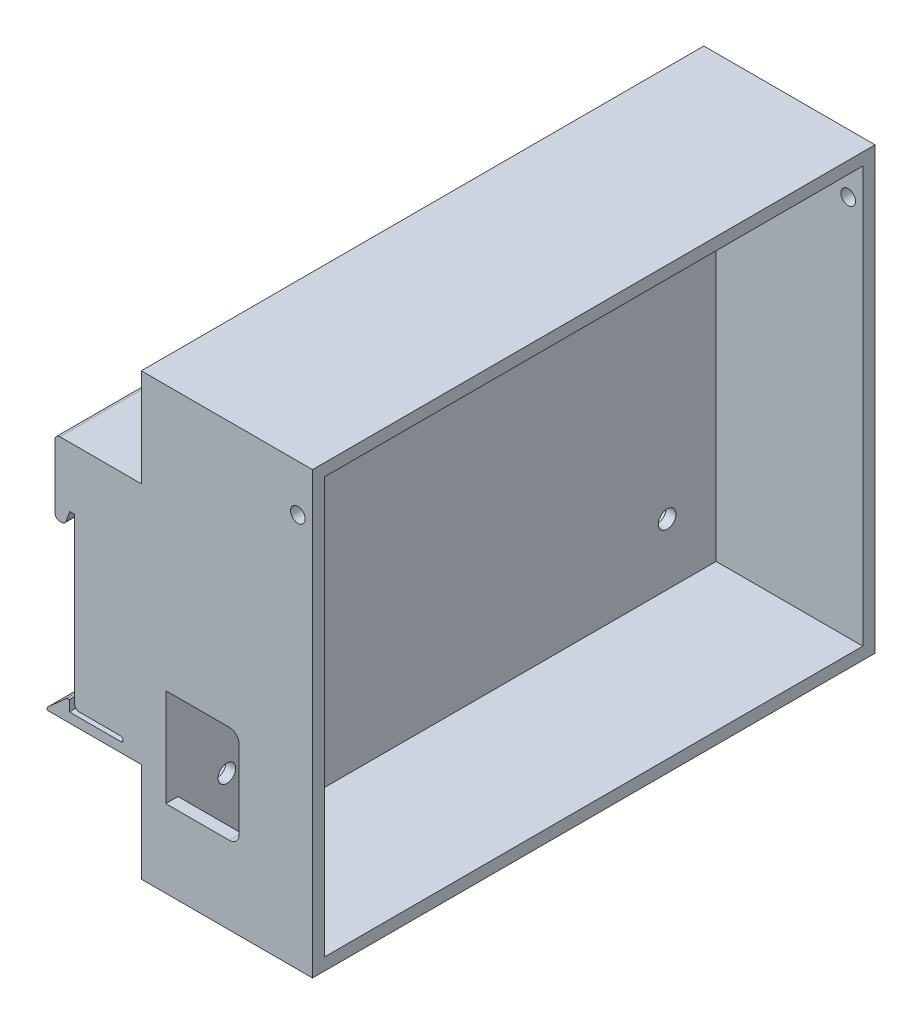
SolidWorks part; units mm, degrees
ref_plane "Alzado" through (0, 0, 0) normal (0, 0, 1) x (1, 0, 0)
ref_plane "Planta" through (0, 0, 0) normal (0, 1, 0) x (1, 0, 0)
ref_plane "Vista lateral" through (0, 0, 0) normal (1, 0, 0) x (0, 0, -1)
sketch "Croquis1" plane through (0, 0, 0) normal (0, 0, 1) x (1, 0, 0)
  line L0 (0, 49.71) -> (-16.64, 49.71)
  line L1 (0, 0) -> (-19.29, 0)
  line L2 (0, 0) -> (0, 49.71)
  line L3 (-17.64, 48.71) -> (-17.64, 35.71)
  line L4 (-16.3226, 34.71) -> (-16.64, 34.71)
  line L6 (-14.64, 37.46) -> (-13.64, 37.46)
  line L7 (-13.64, 37.46) -> (-13.64, 3.96)
  line L8 (-19.29, 0) -> (-19.29, 0.0511)
  line L9 (-14.72, 4.12) -> (-14.72, 1.96)
  line L10 (-14.72, 1.96) -> (-4.22, 1.96)
  line L11 (0, 0) -> (-19.29, 0)
  line L12 (-14.8396, 4.12) -> (-14.72, 4.12)
  line L13 (-4.22, 1.96) -> (-4.22, 2.46)
  line L14 (-10.6248, 33.7424) -> (-10.6723, 33.801)
  line L15 (-4.22, 2.96) -> (-12.64, 2.96)
  line L16 (-14.72, 4.12) -> (-15.22, 4.12)
  line L17 (-19.29, 0) -> (-19.29, 0.5)
  line L18 (-18.9546, 0.7983) -> (-15.5042, 3.8672)
  line L19 (-15.3803, 35.3754) -> (-14.64, 37.46)
  arc A0 (-4.22, 1.96) -> (-4.22, 2.96) centre (-4.22, 2.46) ccw
  arc A1 (-19.29, 0.0511) -> (-18.9546, 0.7983) centre (-18.29, 0.0511) cw
  arc A2 (-14.8396, 4.12) -> (-15.5042, 3.8672) centre (-14.8396, 3.12) ccw
  arc A3 (-17.64, 35.71) -> (-16.64, 34.71) centre (-16.64, 35.71) ccw
  arc A4 (-16.3226, 34.71) -> (-15.3803, 35.3754) centre (-16.3226, 35.71) ccw
  arc A5 (-13.64, 3.96) -> (-12.64, 2.96) centre (-12.64, 3.96) ccw
  arc A6 (-16.64, 49.71) -> (-17.64, 48.71) centre (-16.64, 48.71) ccw
  point P27 (-17.64, 34.71)
  point P34 (-17.64, 49.71)
  dimension "D14" = 0.5
  dimension "D11" = 1
  dimension "D5" = 1
  dimension "D6" = 1
  dimension "D1" = 49.71
  dimension "D2" = 19.29
  dimension "D3" = 17.64
  dimension "D4" = 15
  dimension "D7" = 1
  dimension "D8" = 2.16
  dimension "D9" = 10.5
  dimension "D10" = 19.29
  dimension "D13" = 0.5
  dimension "D15" = 0.5
extrude "Saliente-Extruir1" add sketch "Croquis1" along normal blind 115
sketch "Croquis5" plane through (-19.29, 0, 0) normal (-1, 0, 0) x (0, 0, 1)
  line L0 (0, 0) -> (14.9999, 0.0511) construction
  line L1 (115, 0.0511) -> (0, 0.0511) construction
  line L2 (115, 0) -> (100.0001, 0.0511) construction
  line L4 (14.9999, 53.2806) -> (14.9999, -4.0392)
  line L5 (91.0001, 53.2806) -> (91.0001, -4.0392)
  line L9 (14.9999, 53.2806) -> (91.0001, 53.2806)
  line L11 (14.9999, -4.0392) -> (91.0001, -4.0392)
  dimension "D1" = 15
  dimension "D2" = 15
extrude "Cortar-Extruir2" cut sketch "Croquis5" against normal blind 16
sketch "Croquis6" plane through (-3.29, 0, 0) normal (-1, 0, 0) x (0, 0, 1)
  line L1 (14.9999, 49.71) -> (91.0001, 49.71)
  line L2 (14.9999, 49.71) -> (14.9999, 42.21)
  line L3 (14.9999, 42.21) -> (91.0001, 42.21)
  line L4 (91.0001, 49.71) -> (91.0001, 42.21)
  line L5 (91.0001, 48.71) -> (91.0001, 35.71) construction
  line L7 (14.9999, 49.71) -> (14.9999, 0) construction
  line L9 (14.9999, 2.96) -> (90.9999, 2.96)
  line L10 (14.9999, 2.96) -> (14.9999, 10.46)
  line L11 (14.9999, 10.46) -> (90.9999, 10.46)
  line L12 (14.9999, 0) -> (14.9999, 2.96) construction
  line L13 (90.9999, 2.96) -> (90.9999, 10.46)
  dimension "D1" = 7.5
  dimension "D2" = 7.5
  dimension "D3" = 76
  dimension "D4" = 2.96
extrude "Saliente-Extruir2" add sketch "Croquis6" along normal up to surface (10.35 mm away) up to face at (-13.64, 20.71, 103)
fillet "Redondeo1" radius 1 1 edges at (-13.64, 2.96, 52.9999)
sketch "Croquis7" plane through (0, 0, 0) normal (1, 0, 0) x (0, 0, -1)
  line L2 (-115, 0) -> (-115, -19.29) construction
  line L3 (-115, 49.71) -> (-115, 69.71) construction
  line L5 (-115, 69.71) -> (0, 69.71)
  line L6 (-115, 69.71) -> (-115, -20.29)
  line L7 (-115, -20.29) -> (0, -20.29)
  line L8 (0, 69.71) -> (0, -20.29)
  dimension "D1" = 19.29
  dimension "D2" = 20
  dimension "D3" = 90
extrude "Saliente-Extruir3" add sketch "Croquis7" along normal blind 5
sketch "Croquis14" plane through (5, 0, 0) normal (1, 0, 0) x (0, 0, -1)
  line L0 (-115, 69.71) -> (-112.5, 69.71) construction
  line L1 (0, 69.71) -> (-115, 69.71) construction
  line L2 (-112.5, 69.71) -> (-112.5, 67.21) construction
  line L4 (-112.5, 67.21) -> (-2.5, 67.21)
  line L5 (-112.5, 67.21) -> (-112.5, -17.79)
  line L6 (-112.5, -17.79) -> (-2.5, -17.79)
  line L7 (-2.5, 67.21) -> (-2.5, -17.79)
  line L8 (-115, 69.71) -> (0, 69.71)
  line L9 (-115, 69.71) -> (-115, -20.29)
  line L10 (-115, -20.29) -> (0, -20.29)
  line L11 (0, 69.71) -> (0, -20.29)
  dimension "D1" = 2.5
  dimension "D2" = 2.5
  dimension "D3" = 85
  dimension "D4" = 110
extrude "Saliente-Extruir5" add sketch "Croquis14" along normal blind 30
sketch "Croquis15" plane through (5, 0, 0) normal (1, 0, 0) x (0, 0, -1)
  line L0 (-112.5, 67.21) -> (-102.5, 67.21) construction
  line L1 (-2.5, 67.21) -> (-112.5, 67.21) construction
  line L2 (-102.5, 67.21) -> (-102.5, 54.71) construction
  line L3 (-112.5, 24.71) -> (1.5061, 24.71) construction
  line L4 (-112.5, 67.21) -> (-112.5, -17.79) construction
  line L5 (-57.5, 67.21) -> (-57.5, -22.9682) construction
  circle A0 centre (-102.5, 54.71) radius 1.8
  circle A1 centre (-102.5, -5.29) radius 1.8
  circle A2 centre (-12.5, -5.29) radius 1.8
  circle A3 centre (-12.5, 54.71) radius 1.8
  dimension "D3" = 3.6
  dimension "D1" = 10
  dimension "D2" = 12.5
extrude "Cortar-Extruir5" cut sketch "Croquis15" against normal up to next
sketch "Croquis16" plane through (0, 0, 112.5) normal (0, 0, -1) x (-1, 0, 0)
  line L0 (-5, -17.79) -> (-5, -5.79)
  line L1 (-5, 67.21) -> (-5, -17.79) construction
  line L2 (-5, 15.585) -> (-5, -4.415)
  line L3 (-5, 14.21) -> (-5, 15.585) construction
  line L4 (-5, 15.585) -> (-18, 15.585)
  line L6 (-5, -5.79) -> (-5, -4.415) construction
  line L7 (-5, -4.415) -> (-18, -4.415)
  line L8 (-20, -2.415) -> (-20, 13.585)
  arc A0 (-18, -4.415) -> (-20, -2.415) centre (-18, -2.415) cw
  arc A1 (-18, 15.585) -> (-20, 13.585) centre (-18, 13.585) ccw
  point P10 (-20, -5.79)
  point P13 (-20, 14.21)
  line M7 (-5, -17.79) -> (-5, 67.21)
  dimension "D4" = 1.375
  dimension "D6" = 2
  dimension "D1" = 12
  dimension "D2" = 15
  dimension "D3" = 20
  dimension "D5" = 1.375
extrude "Cortar-Extruir6" cut sketch "Croquis16" against normal up to next contours L4 A1 L8 A0 L7 M7
sketch "Croquis17" plane through (0, 0, 0) normal (-1, 0, 0) x (0, 0, 1)
  line L0 (57.5, 69.71) -> (57.5, -20.29) construction
  line L1 (12.5, 51.2459) -> (15.5, 52.9779)
  line L2 (15.5, 52.9779) -> (15.5, 56.4421)
  line L3 (15.5, 56.4421) -> (12.5, 58.1741)
  line L4 (12.5, 58.1741) -> (9.5, 56.4421)
  line L5 (9.5, 56.4421) -> (9.5, 52.9779)
  line L6 (9.5, 52.9779) -> (12.5, 51.2459)
  line L9 (0, 69.71) -> (115, 69.71) construction
  line L10 (115, -20.29) -> (0, -20.29) construction
  line L11 (57.5, 24.71) -> (0, 24.71) construction
  line L12 (0, 37.46) -> (0, 3.96) construction
  line L13 (9.5, -3.5579) -> (12.5, -1.8259)
  line L14 (9.5, -7.0221) -> (9.5, -3.5579)
  line L15 (12.5, -8.7541) -> (9.5, -7.0221)
  line L16 (15.5, -7.0221) -> (12.5, -8.7541)
  line L17 (15.5, -3.5579) -> (15.5, -7.0221)
  line L18 (12.5, -1.8259) -> (15.5, -3.5579)
  line L19 (105.5, 52.9779) -> (102.5, 51.2459)
  line L20 (105.5, 56.4421) -> (105.5, 52.9779)
  line L21 (102.5, 58.1741) -> (105.5, 56.4421)
  line L22 (99.5, 56.4421) -> (102.5, 58.1741)
  line L23 (99.5, 52.9779) -> (99.5, 56.4421)
  line L24 (102.5, 51.2459) -> (99.5, 52.9779)
  line L25 (102.5, -1.8259) -> (99.5, -3.5579)
  line L26 (99.5, -3.5579) -> (99.5, -7.0221)
  line L27 (99.5, -7.0221) -> (102.5, -8.7541)
  line L28 (102.5, -8.7541) -> (105.5, -7.0221)
  line L29 (105.5, -7.0221) -> (105.5, -3.5579)
  line L30 (105.5, -3.5579) -> (102.5, -1.8259)
  circle A0 centre (12.5, 54.71) radius 3 construction
  circle A1 centre (12.5, -5.29) radius 3 construction
  circle A2 centre (102.5, 54.71) radius 3 construction
  circle A3 centre (102.5, -5.29) radius 3 construction
extrude "Cortar-Extruir7" cut sketch "Croquis17" against normal blind 3
sketch "Croquis19" plane through (0, 0, 0) normal (0, 0, -1) x (-1, 0, 0)
  line L0 (-35, 69.71) -> (-32, 69.71) construction
  line L1 (-35, 69.71) -> (0, 69.71) construction
  line L2 (-32, 69.71) -> (-32, 60.21) construction
  circle A0 centre (-32, 60.21) radius 1.5
  dimension "D3" = 3
  dimension "D1" = 3
  dimension "D2" = 9.5
extrude "Cortar-Extruir8" cut sketch "Croquis19" against normal through all
